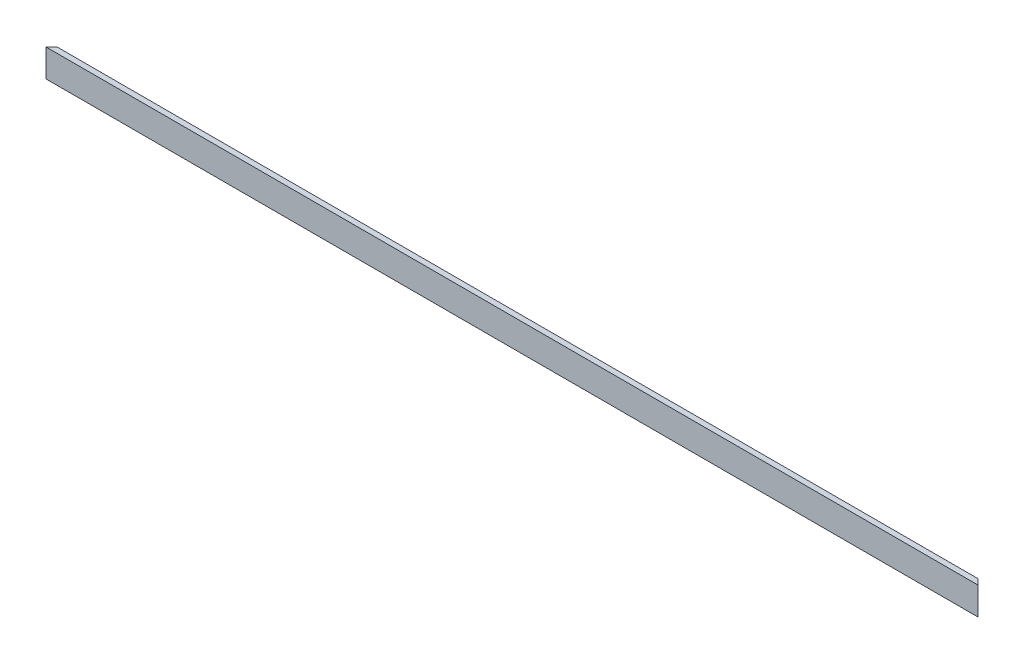
SolidWorks part; units mm, degrees
ref_plane "Front Plane" through (0, 0, 0) normal (0, 0, 1) x (1, 0, 0)
ref_plane "Top Plane" through (0, 0, 0) normal (0, 1, 0) x (1, 0, 0)
ref_plane "Right Plane" through (0, 0, 0) normal (1, 0, 0) x (0, 0, -1)
sketch "Sketch1" plane through (0, 0, 0) normal (0, 0, 1) x (1, 0, 0)
  line L1 (0, 0) -> (6406.9631, 0)
  line L2 (0, 0) -> (0, 190.5)
  line L3 (0, 190.5) -> (6406.9631, 190.5)
  line L4 (6406.9631, 0) -> (6406.9631, 190.5)
  dimension "D1" = 6406.9631
  dimension "D2" = 190.5
extrude "Boss-Extrude1" add sketch "Sketch1" along normal blind 38.1
sketch "Sketch2" plane through (0, 190.5, 0) normal (0, 1, 0) x (1, 0, 0)
  line L0 (0, -38.1) -> (38.1, 0)
  line L1 (6406.9631, 0) -> (0, 0) construction
  line L2 (38.1, 0) -> (0, 0)
  line L3 (0, 0) -> (0, -38.1)
  line L4 (6406.9631, -38.1) -> (6368.8631, 0)
  line L5 (6368.8631, 0) -> (6406.9631, 0)
  line L6 (6406.9631, 0) -> (6406.9631, -38.1)
extrude "Cut-Extrude1" cut sketch "Sketch2" against normal up to surface (190.5 mm away) up to face at (3203.4815, 0, 19.05)
